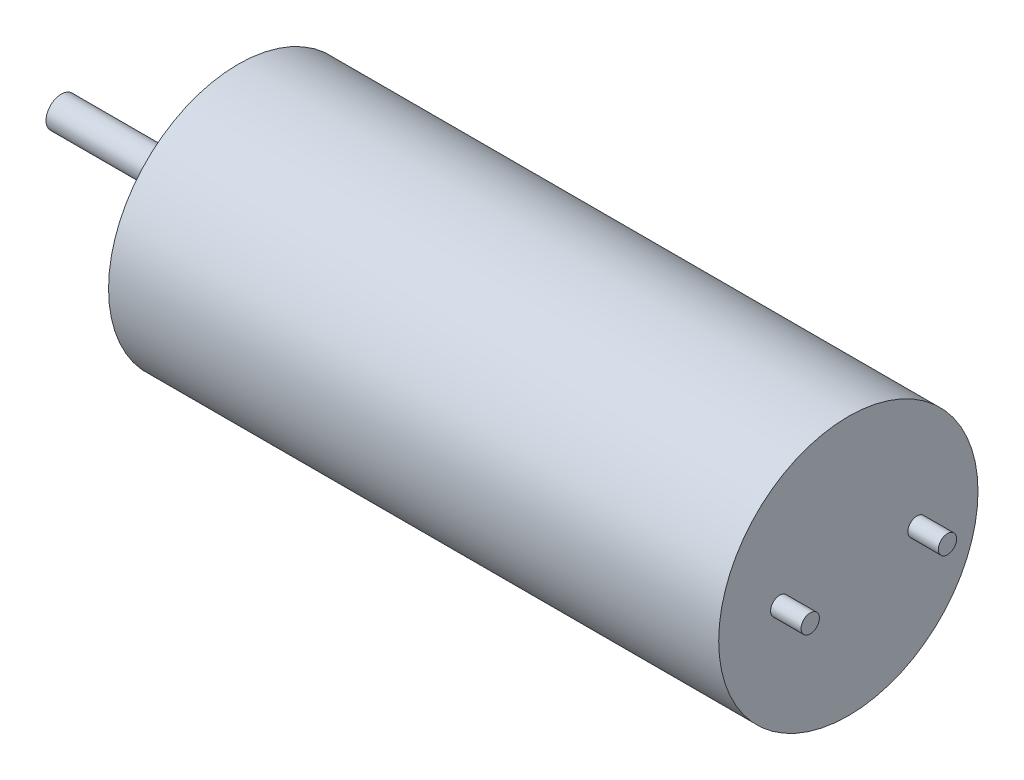
SolidWorks part; units mm, degrees
ref_plane "Front Plane" through (0, 0, 0) normal (0, 0, 1) x (1, 0, 0)
ref_plane "Top Plane" through (0, 0, 0) normal (0, 1, 0) x (1, 0, 0)
ref_plane "Right Plane" through (0, 0, 0) normal (1, 0, 0) x (0, 0, -1)
sketch "Sketch1" plane through (0, 0, 0) normal (1, 0, 0) x (0, 0, -1)
  circle A0 centre (0, 0) radius 4.25
  dimension "D1" = 8.5
extrude "Boss-Extrude1" add sketch "Sketch1" along normal blind 20
sketch "Sketch2" plane through (0, 0, 0) normal (-1, 0, 0) x (0, 0, 1)
  circle A0 centre (0, 0) radius 1.2
  dimension "D1" = 2.4
extrude "Boss-Extrude2" add sketch "Sketch2" along normal blind 0.8
sketch "Sketch3" plane through (-0.8, 0, 0) normal (-1, 0, 0) x (0, 0, 1)
  circle A0 centre (0, 0) radius 0.5
  dimension "D1" = 1
extrude "Boss-Extrude3" add sketch "Sketch3" along normal blind 5
sketch "Sketch4" plane through (20, 0, 0) normal (1, 0, 0) x (0, 0, -1)
  line L0 (-2.25, 0) -> (2.25, 0) construction
  circle A0 centre (-2.25, 0) radius 0.3
  circle A1 centre (2.25, 0) radius 0.3
  point P4 (0, 0)
  dimension "D2" = 0.6
  dimension "D1" = 4.5
extrude "Boss-Extrude4" add sketch "Sketch4" along normal blind 1
